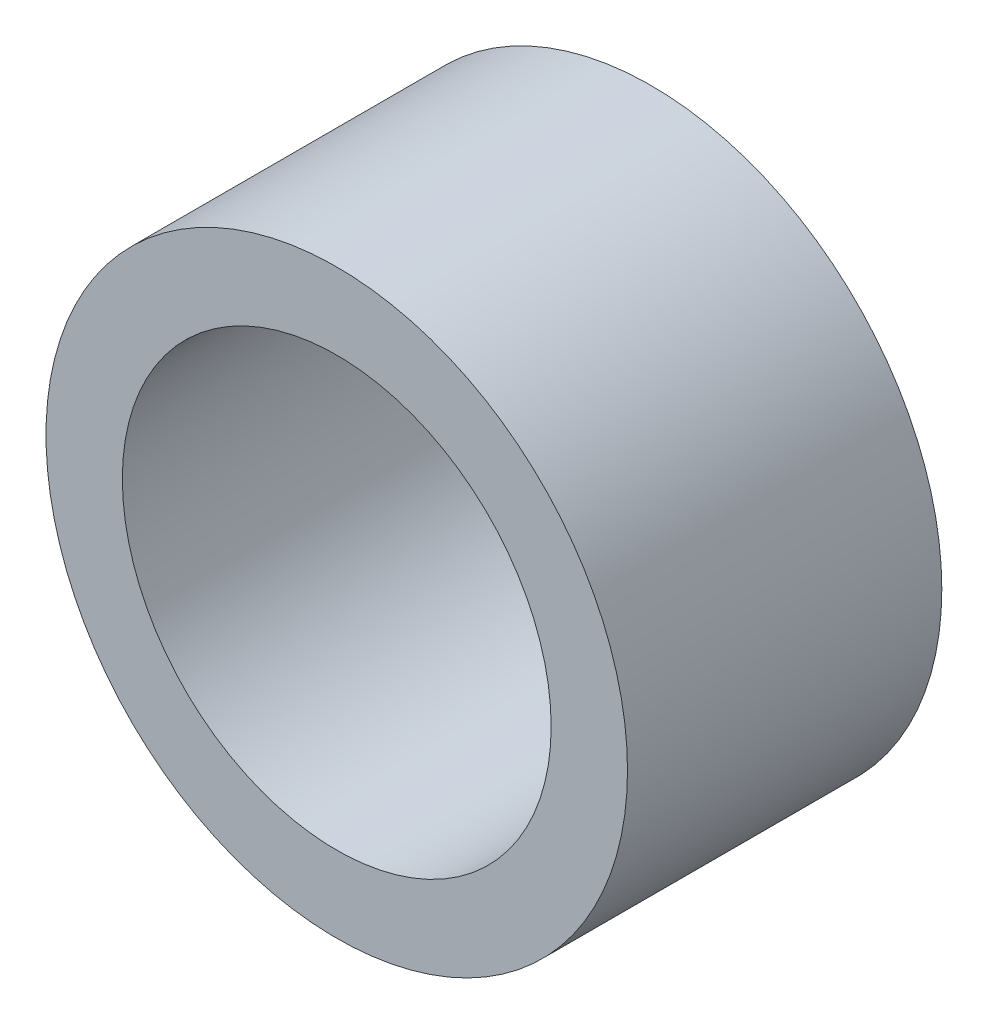
SolidWorks part; units mm, degrees
ref_plane "Front Plane" through (0, 0, 0) normal (0, 0, 1) x (1, 0, 0)
ref_plane "Top Plane" through (0, 0, 0) normal (0, 1, 0) x (1, 0, 0)
ref_plane "Right Plane" through (0, 0, 0) normal (1, 0, 0) x (0, 0, -1)
sketch "Sketch1" plane through (0, 0, 0) normal (0, 0, 1) x (1, 0, 0)
  circle A0 centre (0, 0) radius 4.8514
  circle A1 centre (0, 0) radius 6.5786
  dimension "D1" = 9.7028
  dimension "D2" = 13.1572
extrude "Boss-Extrude1" add sketch "Sketch1" along normal blind 7.112
